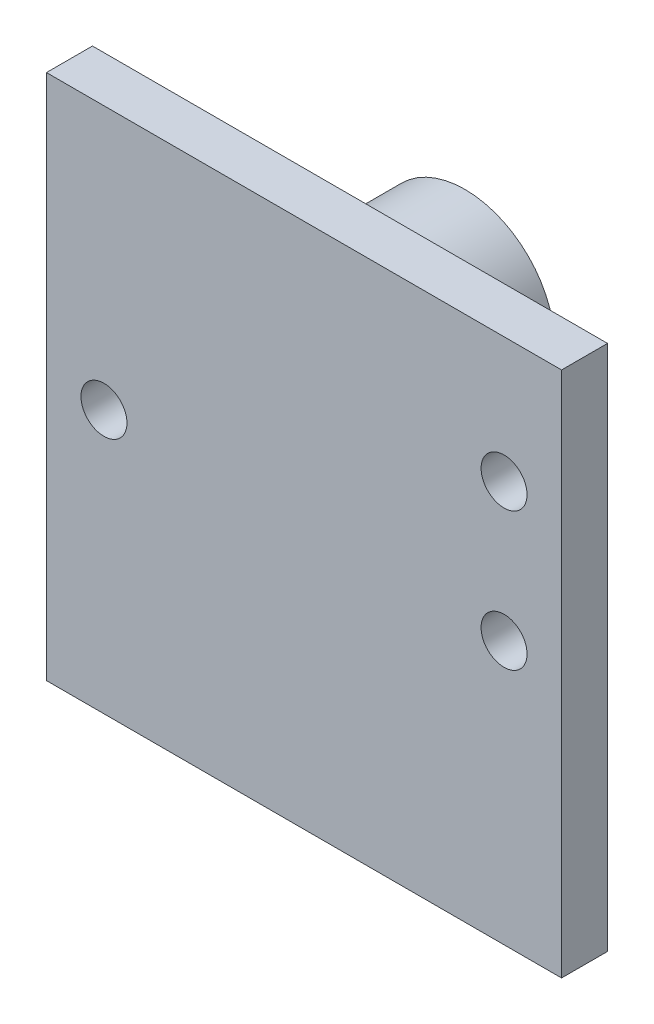
SolidWorks part; units mm, degrees
ref_plane "Front Plane" through (0, 0, 0) normal (0, 0, 1) x (1, 0, 0)
ref_plane "Top Plane" through (0, 0, 0) normal (0, 1, 0) x (1, 0, 0)
ref_plane "Right Plane" through (0, 0, 0) normal (1, 0, 0) x (0, 0, -1)
sketch "Sketch1" plane through (0, 0, 0) normal (0, 0, 1) x (1, 0, 0)
  line L1 (-11.2, 11.45) -> (11.2, 11.45)
  line L2 (-11.2, 11.45) -> (-11.2, -11.45)
  line L3 (-11.2, -11.45) -> (11.2, -11.45)
  line L4 (11.2, 11.45) -> (11.2, -11.45)
  line L5 (-11.2, 11.45) -> (11.2, -11.45) construction
  line L6 (-11.2, -11.45) -> (11.2, 11.45) construction
  point P0 (0, 0)
  dimension "D1" = 22.4
  dimension "D2" = 22.9
extrude "Boss-Extrude1" add sketch "Sketch1" along normal blind 2
sketch "Sketch2" plane through (0, 0, 2) normal (0, 0, 1) x (1, 0, 0)
  line L0 (0, 0) -> (-11.2, 0) construction
  line L1 (-11.2, 11.45) -> (-11.2, -11.45) construction
  line L2 (0, 0) -> (11.2, 0) construction
  line L3 (11.2, -11.45) -> (11.2, 11.45) construction
  line L4 (-11.2, 11.45) -> (-8.7, 11.45) construction
  line L5 (11.2, 11.45) -> (-11.2, 11.45) construction
  line L6 (11.2, 11.45) -> (8.7, 11.45) construction
  line L7 (-8.7, 11.45) -> (-8.7, 0) construction
  line L8 (8.7, 11.45) -> (8.7, 0) construction
  line L9 (8.7, 0) -> (8.7, 6) construction
  circle A0 centre (-8.7, 0) radius 1
  circle A1 centre (8.7, 0) radius 1
  circle A2 centre (8.7, 6) radius 1
  dimension "D3" = 6
  dimension "D1" = 2.5
  dimension "D2" = 2.5
extrude "Cut-Extrude1" cut sketch "Sketch2" against normal blind 5
sketch "Sketch4" plane through (0, 0, 0) normal (0, 0, -1) x (-1, 0, 0)
  line L0 (-11.2, 11.45) -> (11.2, 11.45) construction
  line L1 (-11.2, 11.45) -> (11.2, 11.45) construction
  line L2 (0, 11.45) -> (0, 5.25) construction
  circle A0 centre (0, 5.25) radius 3.9
  dimension "D1" = 6.2
extrude "Boss-Extrude3" add sketch "Sketch4" along normal blind 5 contours A0
